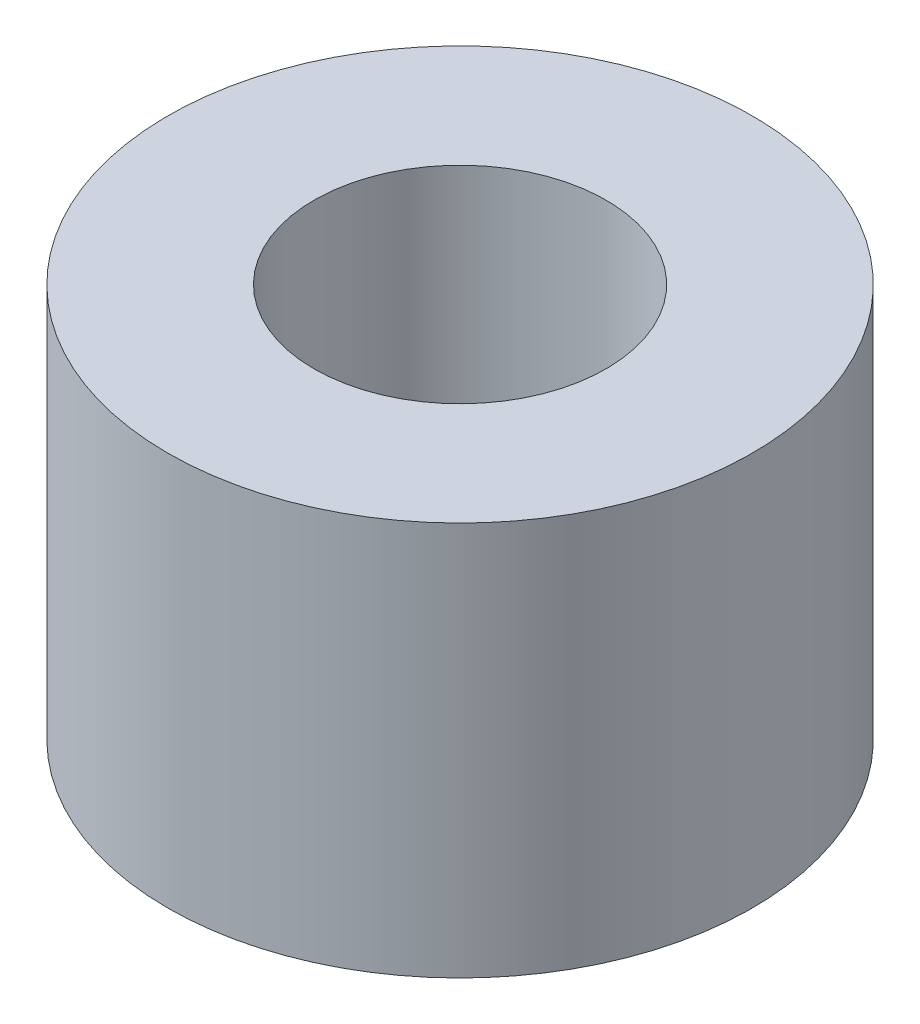
SolidWorks part; units mm, degrees
material "6061-T6 (SS)"
ref_plane "Front" through (0, 0, 0) normal (0, 0, 1) x (1, 0, 0)
ref_plane "Top" through (0, 0, 0) normal (0, 1, 0) x (1, 0, 0)
ref_plane "Right" through (0, 0, 0) normal (1, 0, 0) x (0, 0, -1)
sketch "Sketch1" plane through (0, 0, 0) normal (0, 1, 0) x (1, 0, 0)
  circle A0 centre (0, 0) radius 6.35
  circle A1 centre (0, 0) radius 3.175
  dimension "D1" = 12.7
  dimension "D2" = 6.35
extrude "Boss-Extrude1" add sketch "Sketch1" along normal blind 8.5623
